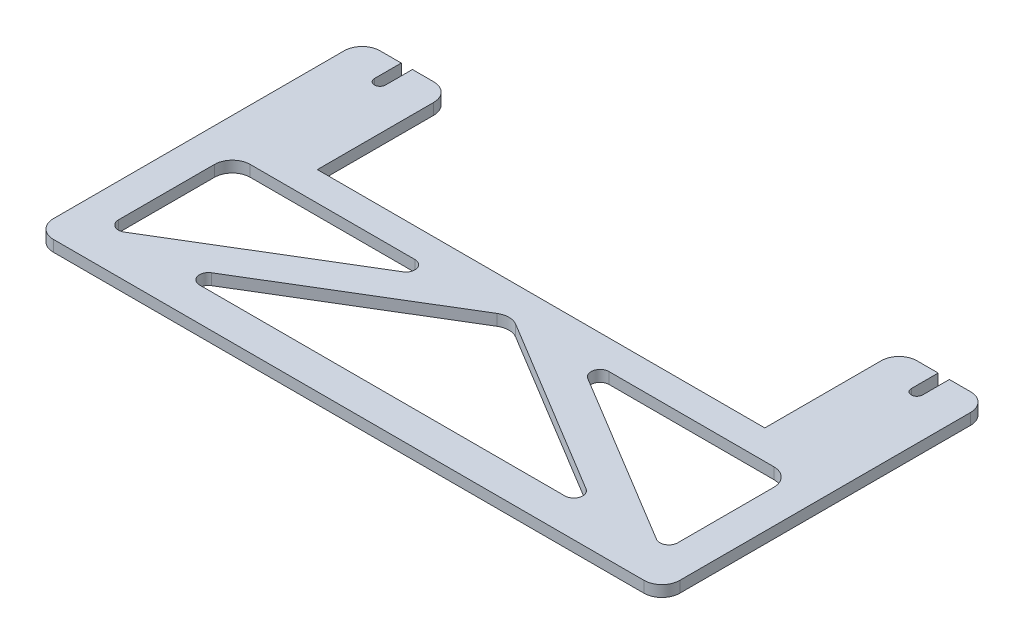
SolidWorks part; units mm, degrees
ref_plane "Front Plane" through (0, 0, 0) normal (0, 0, 1) x (1, 0, 0)
ref_plane "Top Plane" through (0, 0, 0) normal (0, 1, 0) x (1, 0, 0)
ref_plane "Right Plane" through (0, 0, 0) normal (1, 0, 0) x (0, 0, -1)
sketch "Sketch1" plane through (0, 0, 0) normal (0, 1, 0) x (1, 0, 0)
  line L1 (0, 0) -> (177.8, 0)
  line L2 (0, 0) -> (0, 67.31)
  line L3 (0, 67.31) -> (177.8, 67.31)
  line L4 (177.8, 0) -> (177.8, 67.31)
  dimension "D1" = 177.8
  dimension "D2" = 67.31
extrude "Boss-Extrude1" add sketch "Sketch1" along normal blind 3.175
sketch "Sketch3" plane through (0, 3.175, 0) normal (0, 1, 0) x (1, 0, 0)
  line L0 (88.9, 67.31) -> (88.9, 0) construction
  line L1 (177.8, 67.31) -> (0, 67.31) construction
  line L2 (0, 0) -> (177.8, 0) construction
  line L3 (88.9, 46.355) -> (27.9437, 9.525)
  line L4 (27.9437, 9.525) -> (149.8563, 9.525)
  line L5 (9.525, 46.355) -> (9.525, 9.525)
  line L6 (9.525, 9.525) -> (70.4813, 46.355)
  line L7 (70.4813, 46.355) -> (9.525, 46.355)
  line L8 (0, 67.31) -> (0, 0) construction
  line L9 (88.9, 46.355) -> (149.8563, 9.525)
  line L10 (168.275, 9.525) -> (107.3187, 46.355)
  line L11 (107.3187, 46.355) -> (168.275, 46.355)
  line L12 (168.275, 46.355) -> (168.275, 9.525)
  point P6 (12.7, 62.23)
  point P7 (165.1, 62.23)
  point P17 (88.9, 9.525)
  dimension "D1" = 152.4
  dimension "D2" = 5.08
  dimension "D3" = 9.525
  dimension "D4" = 9.525
  dimension "D5" = 9.525
  dimension "D6" = 15.875
extrude "Cut-Extrude1" cut sketch "Sketch3" against normal through all
sketch "Sketch4" plane through (0, 3.175, 0) normal (0, 1, 0) x (1, 0, 0)
  line L0 (11.1125, 67.31) -> (11.1125, 62.23)
  line L1 (177.8, 67.31) -> (0, 67.31) construction
  line L2 (14.2875, 62.23) -> (14.2875, 67.31)
  line L3 (11.1125, 67.31) -> (14.2875, 67.31)
  line L4 (88.9, 67.31) -> (88.9, 47.4197) construction
  line L5 (88.9, 67.31) -> (88.9, 0) construction
  line L6 (166.6875, 67.31) -> (166.6875, 62.23)
  line L7 (163.5125, 62.23) -> (163.5125, 67.31)
  line L8 (166.6875, 67.31) -> (163.5125, 67.31)
  arc A0 (11.1125, 62.23) -> (14.2875, 62.23) centre (12.7, 62.23) ccw
  arc A1 (166.6875, 62.23) -> (163.5125, 62.23) centre (165.1, 62.23) cw
  dimension "D1" = 3.175
extrude "Cut-Extrude2" cut sketch "Sketch4" against normal through all
sketch "Sketch5" plane through (0, 3.175, 0) normal (0, 1, 0) x (1, 0, 0)
  line L0 (25.4, 67.31) -> (25.4, 54.61)
  line L1 (163.5125, 67.31) -> (14.2875, 67.31) construction
  line L2 (25.4, 54.61) -> (152.4, 54.61)
  line L3 (152.4, 54.61) -> (152.4, 67.31)
  line L4 (152.4, 67.31) -> (25.4, 67.31)
  line L7 (88.9, 67.31) -> (88.9, 90.0705) construction
  dimension "D1" = 12.7
  dimension "D2" = 12.7
extrude "Cut-Extrude3" cut sketch "Sketch5" against normal through all
fillet "Fillet1" radius 5.08 9 edges at (88.9, 1.5875, -46.355) (168.275, 1.5875, -46.355) (9.525, 1.5875, -46.355) (152.4, 1.5875, -67.31) (177.8, 1.5875, -67.31) (177.8, 1.5875, 0) (0, 1.5875, 0) (0, 1.5875, -67.31) (25.4, 1.5875, -67.31)
fillet "Fillet2" radius 2.54 6 edges at (107.3187, 1.5875, -46.355) (168.275, 1.5875, -9.525) (149.8563, 1.5875, -9.525) (27.9437, 1.5875, -9.525) (9.525, 1.5875, -9.525) (70.4813, 1.5875, -46.355)
sketch "Sketch6" plane through (0, 3.175, 0) normal (0, 1, 0) x (1, 0, 0)
  line L0 (0, 54.61) -> (177.8, 54.61) construction
  line L1 (0, 62.23) -> (0, 5.08) construction
  line L2 (177.8, 5.08) -> (177.8, 62.23) construction
sketch "Sketch7" plane through (0, 3.175, 0) normal (0, 1, 0) x (1, 0, 0)
  line L0 (0, 54.61) -> (177.8, 54.61) construction
  line L1 (0, 54.61) -> (25.4, 54.61)
  line L2 (0, 54.61) -> (0, 92.71)
  line L3 (0, 92.71) -> (25.4, 92.71)
  line L4 (25.4, 54.61) -> (25.4, 92.71)
  line L5 (152.4, 54.61) -> (177.8, 54.61)
  line L6 (152.4, 54.61) -> (152.4, 92.71)
  line L7 (152.4, 92.71) -> (177.8, 92.71)
  line L8 (177.8, 54.61) -> (177.8, 92.71)
  line L9 (25.4, 62.23) -> (25.4, 54.61) construction
  dimension "D1" = 38.1
extrude "Boss-Extrude2" add sketch "Sketch7" against normal up to surface (3.175 mm away) up to face at (88.9, 0, -52.4831)
sketch "Sketch8" plane through (0, 3.175, 0) normal (0, 1, 0) x (1, 0, 0)
  line L0 (88.9, 54.61) -> (88.9, 78.7147) construction
  line L1 (0, 54.61) -> (177.8, 54.61) construction
  line L2 (25.4, 92.71) -> (0, 92.71) construction
  line L3 (11.1125, 92.71) -> (11.1125, 85.09)
  line L4 (14.2875, 85.09) -> (14.2875, 92.71)
  line L5 (14.2875, 92.71) -> (11.1125, 92.71)
  line L6 (163.5125, 85.09) -> (163.5125, 92.71)
  line L7 (163.5125, 92.71) -> (166.6875, 92.71)
  line L8 (166.6875, 92.71) -> (166.6875, 85.09)
  arc A0 (11.1125, 85.09) -> (14.2875, 85.09) centre (12.7, 85.09) ccw
  arc A1 (166.6875, 85.09) -> (163.5125, 85.09) centre (165.1, 85.09) cw
  point P0 (12.7, 85.09)
  dimension "D1" = 7.62
  dimension "D2" = 3.175
extrude "Cut-Extrude4" cut sketch "Sketch8" against normal through all
fillet "Fillet3" radius 5.08 4 edges at (177.8, 1.5875, -92.71) (152.4, 1.5875, -92.71) (25.4, 1.5875, -92.71) (0, 1.5875, -92.71)
